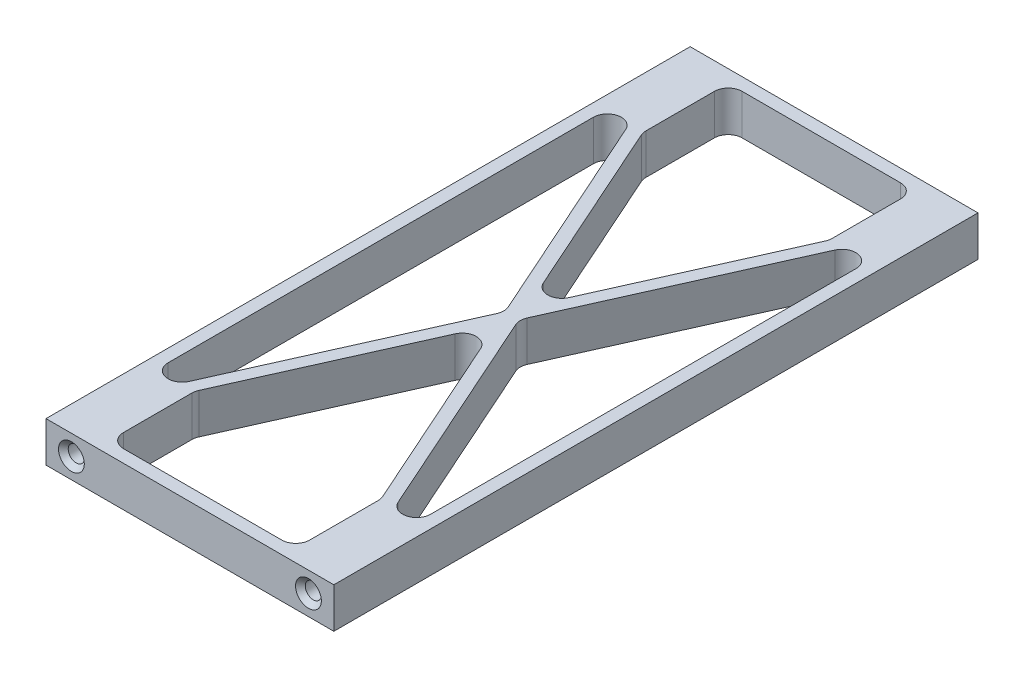
SolidWorks part; units mm, degrees
material "6061-T6 (SS)"
ref_plane "Front Plane" through (0, 0, 0) normal (0, 0, 1) x (1, 0, 0)
ref_plane "Top Plane" through (0, 0, 0) normal (0, 1, 0) x (1, 0, 0)
ref_plane "Right Plane" through (0, 0, 0) normal (1, 0, 0) x (0, 0, -1)
sketch "Sketch1" plane through (0, 0, 0) normal (0, 1, 0) x (1, 0, 0)
  line L1 (-34, -76.0905) -> (34, -76.0905)
  line L2 (-34, -76.0905) -> (-34, 76.0905)
  line L3 (-34, 76.0905) -> (34, 76.0905)
  line L4 (34, -76.0905) -> (34, 76.0905)
  line L5 (-34, -76.0905) -> (34, 76.0905) construction
  line L6 (-34, 76.0905) -> (34, -76.0905) construction
  point P0 (0, 0)
  dimension "D1" = 68
  dimension "D2" = 152.1811
extrude "Boss-Extrude1" add sketch "Sketch1" along normal mid plane 9.525
sketch "Sketch5" plane through (0, 4.7625, 0) normal (0, 1, 0) x (1, 0, 0)
  line L0 (0, 0) -> (10.6371, 0) construction
  line L1 (0, 0) -> (-34, -76.0905) construction
  line L2 (0, 0) -> (-34, 0) construction
  line L3 (-34, 76.0905) -> (-34, -76.0905) construction
  line L4 (-31, -65.6999) -> (-31, 0)
  line L5 (-31, 0) -> (-1.6429, 0)
  line L6 (-1.6429, 0) -> (-31, -65.6999)
  line L7 (-22, -73.0905) -> (0, -73.0905)
  line L8 (0, -73.0905) -> (0, -3.6768)
  line L9 (0, -3.6768) -> (-22, -52.9119)
  line L10 (-34, -76.0905) -> (34, -76.0905) construction
  line L11 (0, 0) -> (0, 22.8457) construction
  line L12 (-22, -73.0905) -> (-22, -52.9119)
  dimension "D1" = 3
  dimension "D2" = 3
  dimension "D3" = 3
  dimension "D4" = 3
  dimension "D5" = 12
extrude "Cut-Extrude2" cut sketch "Sketch5" against normal through all
mirror "Mirror2" about plane through (0, 0, 0) normal (1, 0, 0) of "Cut-Extrude2"
mirror "Mirror3" about plane through (0, 0, 0) normal (0, 0, 1) of "Mirror2", "Cut-Extrude2"
fillet "Fillet1" radius 3.3 16 edges at (31, 0, 65.6999) (1.6429, 0, 0) (31, 0, -65.6999) (0, 0, -3.6768) (0, 0, 3.6768) (-1.6429, 0, 0) (-31, 0, -65.6999) (-31, 0, 65.6999) (22, 0, -73.0905) (22, 0, -52.9119) (-22, 0, -52.9119) (-22, 0, -73.0905) (22, 0, 52.9119) (22, 0, 73.0905) (-22, 0, 52.9119) (-22, 0, 73.0905)
hole_wizard "#10-24 Tapped Hole1" positions "Sketch3" profile "Sketch2" tap size "#10-24" standard "ANSI Inch"
sketch "Sketch3" plane through (0, 0, 76.0905) normal (0, 0, 1) x (1, 0, 0)
  line L0 (0, 0) -> (0, -9.1621) construction
  line L2 (-28, 0) -> (0, 0) construction
  point P0 (-28, 0)
  point P12 (28, 0)
  dimension "D1" = 56
sketch "Sketch2" plane through (-28, 0, 76.0905) normal (1, 0, 0) x (0, -1, 0)
  line L0 (0, 0) -> (0, 16.0908)
  line L1 (0, 16.0908) -> (1.8986, 14.95)
  line L2 (1.8986, 14.95) -> (1.8986, 1.1494)
  line L3 (1.8986, 1.1494) -> (3.048, 0)
  line L5 (3.048, 0) -> (0, 0)
  line L6 (-1.8986, 1.1494) -> (-3.048, 0) construction
  line L10 (0, 16.0908) -> (-1.8987, 14.95) construction
  line L11 (0, -6.35) -> (0, 107.95) construction
  dimension "Tap Drill Dia." = 3.7973
  dimension "Tap Drill Depth" = 14.95
  dimension "Near C'Sink Dia." = 6.096
  dimension "Near C'Sink Angle" = 90
  dimension "Drill Angle" = 118
cosmetic thread "Hole Thread1" parameters "D1"=9.65, "D2"=4.826
cosmetic thread "Hole Thread2" parameters "D1"=9.65, "D2"=4.826
mirror "Mirror1" about plane through (0, 0, 0) normal (0, 0, 1) of "#10-24 Tapped Hole1"
